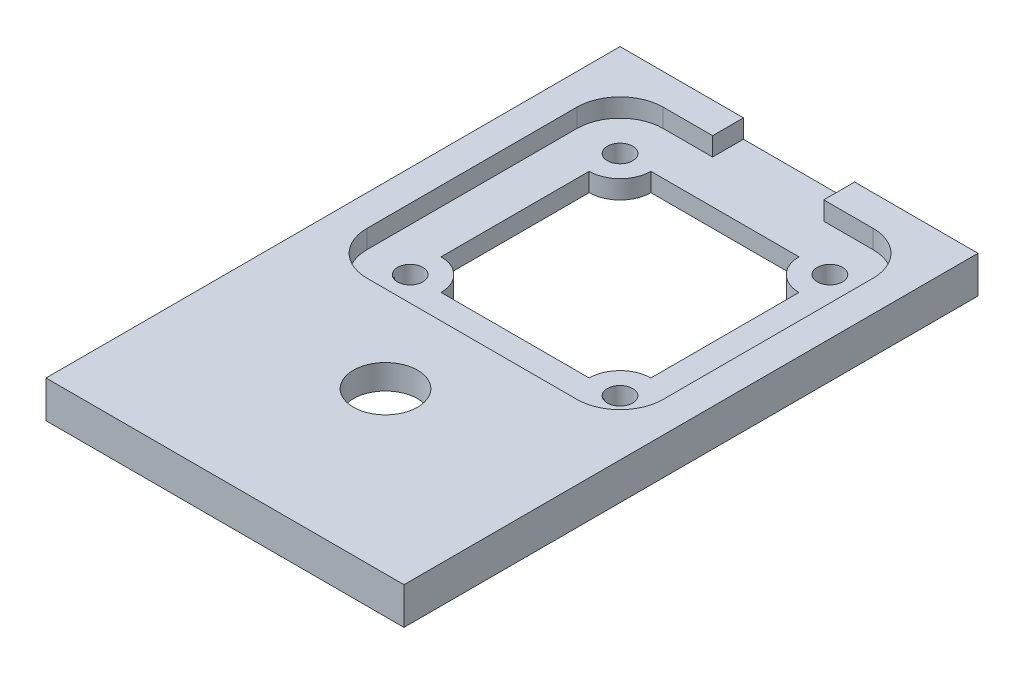
SolidWorks part; units mm, degrees
ref_plane "Front Plane" through (0, 0, 0) normal (0, 0, 1) x (1, 0, 0)
ref_plane "Top Plane" through (0, 0, 0) normal (0, 1, 0) x (1, 0, 0)
ref_plane "Right Plane" through (0, 0, 0) normal (1, 0, 0) x (0, 0, -1)
sketch "Sketch2" plane through (0, 0, 0) normal (0, 1, 0) x (1, 0, 0)
  line L0 (-8.4975, -11.4974) -> (8.4975, -11.4974)
  line L1 (-11.5025, 8.5026) -> (-11.5025, -8.5026)
  line L2 (8.5025, 11.5026) -> (-8.5025, 11.5026)
  line L3 (11.4975, -8.4974) -> (11.4975, 8.4974)
  line L4 (0, 11.5026) -> (0, -11.4974) construction
  line L5 (-11.5025, 0) -> (11.4975, 0) construction
  line L6 (0, 11.5026) -> (0, -29) construction
  line L7 (-10, -29) -> (10, -29)
  line L8 (-10, -29) -> (-10, -9)
  line L9 (-10, -9) -> (10, -9)
  line L10 (10, -29) -> (10, -9)
  line L11 (-10, -29) -> (10, -9) construction
  line L12 (-10, -9) -> (10, -29) construction
  line L13 (8.4975, 8.5026) -> (8.4975, -8.4974) construction
  arc A0 (8.4975, -11.4974) -> (11.4975, -8.4974) centre (8.4975, -8.4974) ccw
  arc A1 (-11.5025, -8.5026) -> (-8.4975, -11.4974) centre (-8.5025, -8.4974) ccw
  arc A2 (-8.5025, 11.5026) -> (-11.5025, 8.5026) centre (-8.5025, 8.5026) ccw
  arc A3 (11.4975, 8.4974) -> (8.5025, 11.5026) centre (8.4975, 8.5026) ccw
  circle A4 centre (-8.5025, -8.4974) radius 1.5
  circle A5 centre (8.4975, 8.5026) radius 1.5
  circle A6 centre (8.4975, -8.4974) radius 1.5
  circle A7 centre (-8.5025, 8.5026) radius 1.5
  circle A8 centre (0, -19) radius 2.6
  dimension "D5" = 3
  dimension "D6" = 3
  dimension "D7" = 3
  dimension "D8" = 3
  dimension "D9" = 3
  dimension "D10" = 3
  dimension "D11" = 3
  dimension "D12" = 3
  dimension "D15" = 17
  dimension "D16" = 17
  dimension "D17" = 5.2
  dimension "D20" = 3
  dimension "D1" = 20
  dimension "D2" = 20
  dimension "D3" = 23
  dimension "D4" = 23
  dimension "D13" = 17
  dimension "D14" = 17
  dimension "D18" = 19
  dimension "D19" = 3
sketch "Sketch3" plane through (0, 0, 0) normal (0, 1, 0) x (1, 0, 0)
  line L1 (-14.5025, 14.5026) -> (14.4975, 14.5026)
  line L2 (-14.5025, 14.5026) -> (-14.5025, -32)
  line L3 (-14.5025, -32) -> (14.4975, -32)
  line L4 (-10, -29) -> (10, -29)
  line L5 (10, -29) -> (10, -9)
  line L6 (10, -9) -> (-10, -9)
  line L7 (-10, -9) -> (-10, -29)
  line L8 (-10, -29) -> (10, -29) construction
  line L9 (10, -29) -> (10, -9) construction
  line L10 (10, -9) -> (-10, -9) construction
  line L11 (-10, -9) -> (-10, -29) construction
  line L12 (11.4975, -8.4974) -> (11.4975, 8.4974)
  line L13 (-8.4975, -11.4974) -> (8.4975, -11.4974)
  line L14 (-11.5025, 8.5026) -> (-11.5025, -8.5026)
  line L15 (8.5025, 11.5026) -> (-8.5025, 11.5026)
  line L16 (11.4975, -8.4974) -> (11.4975, 8.4974) construction
  line L17 (-8.4975, -11.4974) -> (8.4975, -11.4974) construction
  line L18 (-11.5025, 8.5026) -> (-11.5025, -8.5026) construction
  line L19 (8.5025, 11.5026) -> (-8.5025, 11.5026) construction
  line L20 (14.4975, 14.5026) -> (14.4975, -32)
  circle A1 centre (-8.5025, 8.5026) radius 1.5
  circle A2 centre (-8.5025, 8.5026) radius 1.5 construction
  circle A3 centre (8.4975, -8.4974) radius 1.5
  circle A4 centre (8.4975, -8.4974) radius 1.5 construction
  circle A5 centre (8.4975, 8.5026) radius 1.5
  circle A6 centre (8.4975, 8.5026) radius 1.5 construction
  circle A7 centre (-8.5025, -8.4974) radius 1.5
  circle A8 centre (-8.5025, -8.4974) radius 1.5 construction
  circle A9 centre (0, -19) radius 2.6
  circle A10 centre (0, -19) radius 2.6
  arc A14 (8.4975, -11.4974) -> (11.4975, -8.4974) centre (8.4975, -8.4974) ccw
  arc A15 (-11.5025, -8.5026) -> (-8.4975, -11.4974) centre (-8.5025, -8.4974) ccw
  arc A16 (-8.5025, 11.5026) -> (-11.5025, 8.5026) centre (-8.5025, 8.5026) ccw
  arc A17 (11.4975, 8.4974) -> (8.5025, 11.5026) centre (8.4975, 8.5026) ccw
  arc A18 (8.4975, -11.4974) -> (11.4975, -8.4974) centre (8.4975, -8.4974) ccw construction
  arc A19 (-11.5025, -8.5026) -> (-8.4975, -11.4974) centre (-8.5025, -8.4974) ccw construction
  arc A20 (-8.5025, 11.5026) -> (-11.5025, 8.5026) centre (-8.5025, 8.5026) ccw construction
  arc A21 (11.4975, 8.4974) -> (8.5025, 11.5026) centre (8.4975, 8.5026) ccw construction
  dimension "D8" = 3
  dimension "D9" = 3
  dimension "D10" = 3
  dimension "D11" = 6
  dimension "D1" = 0
  dimension "D2" = 0
  dimension "D3" = 0
  dimension "D4" = 0
  dimension "D5" = 0
  dimension "D6" = 0
  dimension "D7" = 0
extrude "Boss-Extrude1" add sketch "Sketch3" along normal blind 3
sketch "Sketch4" plane through (0, 0, 0) normal (0, -1, 0) x (1, 0, 0)
  line L0 (-10.2, 29.2) -> (-10.2, 8.8)
  line L1 (-10.2, 8.8) -> (10.2, 8.8)
  line L2 (10.2, 8.8) -> (10.2, 29.2)
  line L3 (10.2, 29.2) -> (-10.2, 29.2)
  line L4 (10, 29) -> (-10, 29)
  line L5 (10, 9) -> (10, 29)
  line L6 (-10, 9) -> (10, 9)
  line L7 (-10, 29) -> (-10, 9)
  line L8 (10, 29) -> (-10, 29) construction
  line L9 (10, 9) -> (10, 29) construction
  line L10 (-10, 9) -> (10, 9) construction
  line L11 (-10, 29) -> (-10, 9) construction
  line L12 (11.4975, -8.4974) -> (11.4975, 8.4974)
  line L13 (8.4975, 11.4974) -> (-8.4975, 11.4974)
  line L14 (-11.5025, 8.5026) -> (-11.5025, -8.5026)
  line L15 (-8.5025, -11.5026) -> (8.5025, -11.5026)
  line L16 (11.4975, -8.4974) -> (11.4975, 8.4974) construction
  line L17 (8.4975, 11.4974) -> (-8.4975, 11.4974) construction
  line L18 (-11.5025, 8.5026) -> (-11.5025, -8.5026) construction
  line L19 (-8.5025, -11.5026) -> (8.5025, -11.5026) construction
  circle A1 centre (-8.5025, -8.5026) radius 1.5
  circle A2 centre (-8.5025, -8.5026) radius 1.5 construction
  circle A3 centre (8.4975, 8.4974) radius 1.5
  circle A4 centre (8.4975, 8.4974) radius 1.5 construction
  circle A5 centre (8.4975, -8.5026) radius 1.5
  circle A6 centre (8.4975, -8.5026) radius 1.5 construction
  circle A7 centre (-8.5025, 8.4974) radius 1.5
  circle A8 centre (-8.5025, 8.4974) radius 1.5 construction
  circle A9 centre (0, 19) radius 2.6
  circle A10 centre (0, 19) radius 2.6 construction
  arc A14 (11.4975, 8.4974) -> (8.4975, 11.4974) centre (8.4975, 8.4974) ccw
  arc A15 (-8.4975, 11.4974) -> (-11.5025, 8.5026) centre (-8.5025, 8.4974) ccw
  arc A16 (-11.5025, -8.5026) -> (-8.5025, -11.5026) centre (-8.5025, -8.5026) ccw
  arc A17 (8.5025, -11.5026) -> (11.4975, -8.4974) centre (8.4975, -8.5026) ccw
  arc A18 (11.4975, 8.4974) -> (8.4975, 11.4974) centre (8.4975, 8.4974) ccw construction
  arc A19 (-8.4975, 11.4974) -> (-11.5025, 8.5026) centre (-8.5025, 8.4974) ccw construction
  arc A20 (-11.5025, -8.5026) -> (-8.5025, -11.5026) centre (-8.5025, -8.5026) ccw construction
  arc A21 (8.5025, -11.5026) -> (11.4975, -8.4974) centre (8.4975, -8.5026) ccw construction
  dimension "D1" = 0
  dimension "D2" = 0
  dimension "D3" = 0
  dimension "D4" = 0
  dimension "D5" = 0
  dimension "D6" = 0
  dimension "D7" = 0
  dimension "D8" = 0.2
extrude "Cut-Extrude1" cut sketch "Sketch4" against normal blind 1
sketch "Sketch5" plane through (0, 3, 0) normal (0, 1, 0) x (1, 0, 0)
  line L0 (8.5029, 12.0026) -> (-8.5025, 12.0026) construction
  line L1 (-12.0025, 8.5026) -> (-12.0025, -8.503)
  line L2 (-8.4971, -11.9974) -> (8.4975, -11.9974)
  line L3 (11.9975, -8.4974) -> (11.9975, 8.497)
  line L4 (-10, -29) -> (10, -29)
  line L5 (10, -29) -> (10, -9)
  line L6 (10, -9) -> (-10, -9)
  line L7 (-10, -9) -> (-10, -29)
  line L8 (-10, -29) -> (10, -29) construction
  line L9 (10, -29) -> (10, -9) construction
  line L10 (10, -9) -> (-10, -9) construction
  line L11 (-10, -9) -> (-10, -29) construction
  line L12 (11.4975, -8.4974) -> (11.4975, 8.4974)
  line L13 (-8.4975, -11.4974) -> (8.4975, -11.4974)
  line L14 (-11.5025, 8.5026) -> (-11.5025, -8.5026)
  line L15 (8.5025, 11.5026) -> (-8.5025, 11.5026)
  line L16 (11.4975, -8.4974) -> (11.4975, 8.4974) construction
  line L17 (-8.4975, -11.4974) -> (8.4975, -11.4974) construction
  line L18 (-11.5025, 8.5026) -> (-11.5025, -8.5026) construction
  line L19 (8.5025, 11.5026) -> (-8.5025, 11.5026) construction
  line L20 (-8.5025, 12.0026) -> (-4.5025, 12.0026)
  line L21 (-4.5025, 12.0026) -> (-4.5025, 14.5026)
  line L22 (14.4975, 14.5026) -> (-14.5025, 14.5026) construction
  line L23 (8.5029, 12.0026) -> (4.5025, 12.0026)
  line L24 (4.5025, 12.0026) -> (4.5025, 14.5026)
  line L25 (4.5025, 14.5026) -> (-4.5025, 14.5026)
  line L26 (0, 0) -> (0, 14.5026) construction
  arc A0 (-8.5025, 12.0026) -> (-12.0025, 8.5026) centre (-8.5025, 8.5026) ccw
  circle A1 centre (-8.5025, 8.5026) radius 1.5
  circle A2 centre (-8.5025, 8.5026) radius 1.5 construction
  circle A3 centre (8.4975, -8.4974) radius 1.5
  circle A4 centre (8.4975, -8.4974) radius 1.5 construction
  circle A5 centre (8.4975, 8.5026) radius 1.5
  circle A6 centre (8.4975, 8.5026) radius 1.5 construction
  circle A7 centre (-8.5025, -8.4974) radius 1.5
  circle A8 centre (-8.5025, -8.4974) radius 1.5 construction
  circle A9 centre (0, -19) radius 2.6
  circle A10 centre (0, -19) radius 2.6 construction
  arc A11 (-12.0025, -8.503) -> (-8.4971, -11.9974) centre (-8.5025, -8.4974) ccw
  arc A12 (8.4975, -11.9974) -> (11.9975, -8.4974) centre (8.4975, -8.4974) ccw
  arc A13 (11.9975, 8.497) -> (8.5029, 12.0026) centre (8.4975, 8.5026) ccw
  arc A14 (8.4975, -11.4974) -> (11.4975, -8.4974) centre (8.4975, -8.4974) ccw
  arc A15 (-11.5025, -8.5026) -> (-8.4975, -11.4974) centre (-8.5025, -8.4974) ccw
  arc A16 (-8.5025, 11.5026) -> (-11.5025, 8.5026) centre (-8.5025, 8.5026) ccw
  arc A17 (11.4975, 8.4974) -> (8.5025, 11.5026) centre (8.4975, 8.5026) ccw
  arc A18 (8.4975, -11.4974) -> (11.4975, -8.4974) centre (8.4975, -8.4974) ccw construction
  arc A19 (-11.5025, -8.5026) -> (-8.4975, -11.4974) centre (-8.5025, -8.4974) ccw construction
  arc A20 (-8.5025, 11.5026) -> (-11.5025, 8.5026) centre (-8.5025, 8.5026) ccw construction
  arc A21 (11.4975, 8.4974) -> (8.5025, 11.5026) centre (8.4975, 8.5026) ccw construction
  point P49 (0, 14.5026)
  dimension "D9" = 4
  dimension "D1" = 0
  dimension "D2" = 0
  dimension "D3" = 0
  dimension "D4" = 0
  dimension "D5" = 0
  dimension "D6" = 0
  dimension "D7" = 0
  dimension "D8" = 0.5
extrude "Cut-Extrude2" cut sketch "Sketch5" against normal blind 1.5
sketch "Sketch6" plane through (0, 1.5, 0) normal (0, 1, 0) x (1, 0, 0)
  line L4 (-10, -29) -> (10, -29)
  line L5 (10, -29) -> (10, -9)
  line L6 (10, -9) -> (-10, -9)
  line L7 (-10, -9) -> (-10, -29)
  line L8 (-10, -29) -> (10, -29) construction
  line L9 (10, -29) -> (10, -9) construction
  line L10 (10, -9) -> (-10, -9) construction
  line L11 (-10, -9) -> (-10, -29) construction
  line L12 (11.4975, -8.4974) -> (11.4975, 8.4974)
  line L13 (-8.4975, -11.4974) -> (8.4975, -11.4974)
  line L14 (-11.5025, 8.5026) -> (-11.5025, -8.5026)
  line L15 (8.5025, 11.5026) -> (-8.5025, 11.5026)
  line L16 (11.4975, -8.4974) -> (11.4975, 8.4974) construction
  line L17 (-8.4975, -11.4974) -> (8.4975, -11.4974) construction
  line L18 (-11.5025, 8.5026) -> (-11.5025, -8.5026) construction
  line L19 (8.5025, 11.5026) -> (-8.5025, 11.5026) construction
  circle A0 centre (-8.5025, 8.5026) radius 1.025
  circle A1 centre (-8.5025, 8.5026) radius 1.5
  circle A2 centre (-8.5025, 8.5026) radius 1.5 construction
  circle A3 centre (8.4975, -8.4974) radius 1.5
  circle A4 centre (8.4975, -8.4974) radius 1.5 construction
  circle A5 centre (8.4975, 8.5026) radius 1.5
  circle A6 centre (8.4975, 8.5026) radius 1.5 construction
  circle A7 centre (-8.5025, -8.4974) radius 1.5
  circle A8 centre (-8.5025, -8.4974) radius 1.5 construction
  circle A9 centre (0, -19) radius 2.6
  circle A10 centre (0, -19) radius 2.6 construction
  circle A11 centre (8.4975, 8.5026) radius 1.025
  circle A12 centre (8.4975, -8.4974) radius 1.025
  circle A13 centre (-8.5025, -8.4974) radius 1.025
  arc A14 (8.4975, -11.4974) -> (11.4975, -8.4974) centre (8.4975, -8.4974) ccw
  arc A15 (-11.5025, -8.5026) -> (-8.4975, -11.4974) centre (-8.5025, -8.4974) ccw
  arc A16 (-8.5025, 11.5026) -> (-11.5025, 8.5026) centre (-8.5025, 8.5026) ccw
  arc A17 (11.4975, 8.4974) -> (8.5025, 11.5026) centre (8.4975, 8.5026) ccw
  arc A18 (8.4975, -11.4974) -> (11.4975, -8.4974) centre (8.4975, -8.4974) ccw construction
  arc A19 (-11.5025, -8.5026) -> (-8.4975, -11.4974) centre (-8.5025, -8.4974) ccw construction
  arc A20 (-8.5025, 11.5026) -> (-11.5025, 8.5026) centre (-8.5025, 8.5026) ccw construction
  arc A21 (11.4975, 8.4974) -> (8.5025, 11.5026) centre (8.4975, 8.5026) ccw construction
  dimension "D8" = 2.05
  dimension "D9" = 2.05
  dimension "D10" = 2.05
  dimension "D11" = 2.05
  dimension "D1" = 0
  dimension "D2" = 0
  dimension "D3" = 0
  dimension "D4" = 0
  dimension "D5" = 0
  dimension "D6" = 0
  dimension "D7" = 0
extrude "Cut-Extrude3" cut sketch "Sketch6" against normal blind 1.5
sketch "Sketch7" plane through (0, 1.5, 0) normal (0, 1, 0) x (1, 0, 0)
  line L1 (-6.0025, 8.5026) -> (5.9975, 8.5026)
  line L2 (8.4975, 6.0026) -> (8.4975, -5.9974)
  line L3 (-6.0025, -8.4974) -> (5.9975, -8.4974)
  line L4 (-10, -29) -> (10, -29)
  line L5 (10, -29) -> (10, -9)
  line L6 (10, -9) -> (-10, -9)
  line L7 (-10, -9) -> (-10, -29)
  line L8 (-10, -29) -> (10, -29) construction
  line L9 (10, -29) -> (10, -9) construction
  line L10 (10, -9) -> (-10, -9) construction
  line L11 (-10, -9) -> (-10, -29) construction
  line L12 (11.4975, -8.4974) -> (11.4975, 8.4974)
  line L13 (-8.4975, -11.4974) -> (8.4975, -11.4974)
  line L14 (-11.5025, 8.5026) -> (-11.5025, -8.5026)
  line L15 (8.5025, 11.5026) -> (-8.5025, 11.5026)
  line L16 (11.4975, -8.4974) -> (11.4975, 8.4974) construction
  line L17 (-8.4975, -11.4974) -> (8.4975, -11.4974) construction
  line L18 (-11.5025, 8.5026) -> (-11.5025, -8.5026) construction
  line L19 (8.5025, 11.5026) -> (-8.5025, 11.5026) construction
  line L20 (-8.5025, 6.0026) -> (-8.5025, -5.9974)
  circle A0 centre (-8.5025, 8.5026) radius 2.5 construction
  circle A1 centre (-8.5025, 8.5026) radius 1.5
  circle A2 centre (-8.5025, 8.5026) radius 1.5 construction
  circle A3 centre (8.4975, -8.4974) radius 1.5
  circle A4 centre (8.4975, -8.4974) radius 1.5 construction
  circle A5 centre (8.4975, 8.5026) radius 1.5
  circle A6 centre (8.4975, 8.5026) radius 1.5 construction
  circle A7 centre (-8.5025, -8.4974) radius 1.5
  circle A8 centre (-8.5025, -8.4974) radius 1.5 construction
  circle A9 centre (0, -19) radius 2.6
  circle A10 centre (0, -19) radius 2.6 construction
  circle A11 centre (8.4975, 8.5026) radius 2.5 construction
  circle A12 centre (8.4975, -8.4974) radius 2.5 construction
  circle A13 centre (-8.5025, -8.4974) radius 2.5 construction
  arc A14 (8.4975, -11.4974) -> (11.4975, -8.4974) centre (8.4975, -8.4974) ccw
  arc A15 (-11.5025, -8.5026) -> (-8.4975, -11.4974) centre (-8.5025, -8.4974) ccw
  arc A16 (-8.5025, 11.5026) -> (-11.5025, 8.5026) centre (-8.5025, 8.5026) ccw
  arc A17 (11.4975, 8.4974) -> (8.5025, 11.5026) centre (8.4975, 8.5026) ccw
  arc A18 (8.4975, -11.4974) -> (11.4975, -8.4974) centre (8.4975, -8.4974) ccw construction
  arc A19 (-11.5025, -8.5026) -> (-8.4975, -11.4974) centre (-8.5025, -8.4974) ccw construction
  arc A20 (-8.5025, 11.5026) -> (-11.5025, 8.5026) centre (-8.5025, 8.5026) ccw construction
  arc A21 (11.4975, 8.4974) -> (8.5025, 11.5026) centre (8.4975, 8.5026) ccw construction
  arc A22 (-6.0025, 8.5026) -> (-8.5025, 6.0026) centre (-8.5025, 8.5026) cw
  arc A23 (-8.5025, -5.9974) -> (-6.0025, -8.4974) centre (-8.5025, -8.4974) cw
  arc A24 (8.4975, -5.9974) -> (5.9975, -8.4974) centre (8.4975, -8.4974) ccw
  arc A25 (5.9975, 8.5026) -> (8.4975, 6.0026) centre (8.4975, 8.5026) ccw
  dimension "D1" = 0
  dimension "D2" = 0
  dimension "D3" = 0
  dimension "D4" = 0
  dimension "D5" = 0
  dimension "D6" = 0
  dimension "D7" = 0
  dimension "D8" = 1
extrude "Cut-Extrude4" cut sketch "Sketch7" against normal blind 1.5
